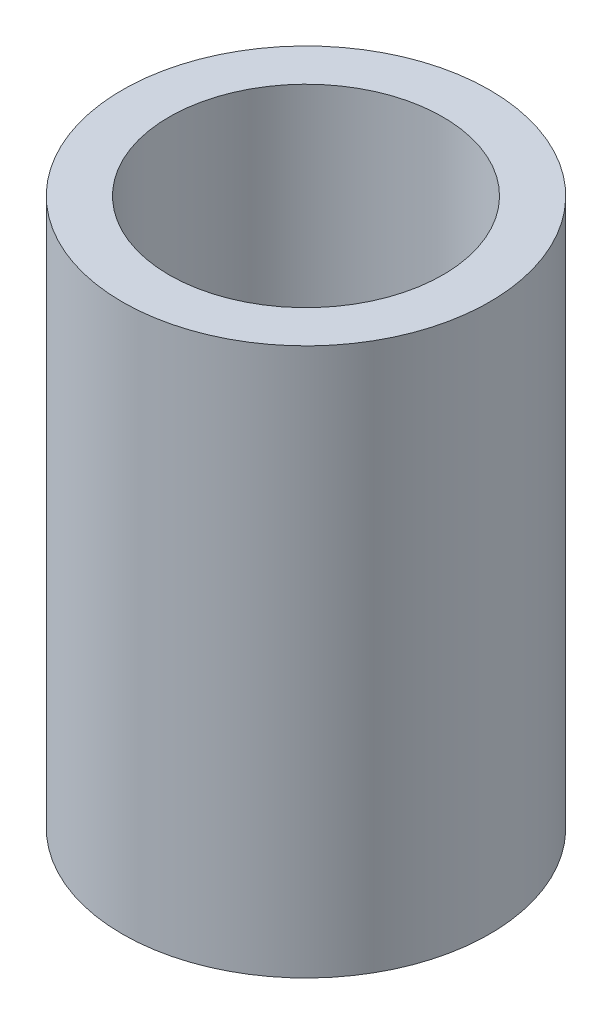
SolidWorks part; units mm, degrees
ref_plane "Front Plane" through (0, 0, 0) normal (0, 0, 1) x (1, 0, 0)
ref_plane "Top Plane" through (0, 0, 0) normal (0, 1, 0) x (1, 0, 0)
ref_plane "Right Plane" through (0, 0, 0) normal (1, 0, 0) x (0, 0, -1)
sketch "Sketch1" plane through (0, 0, 0) normal (0, 0, 1) x (1, 0, 0)
  line L0 (0, 0) -> (0, -62.5229) construction
  line L1 (-38.1, 0) -> (-51.1302, 0)
  line L2 (-38.1, 0) -> (-38.1, -152.4)
  line L3 (-38.1, -152.4) -> (-51.1302, -152.4)
  line L4 (-51.1302, 0) -> (-51.1302, -152.4)
  dimension "D1" = 38.1
  dimension "D2" = 51.1302
  dimension "D3" = 152.4
revolve "Revolve1" add sketch "Sketch1" angle 360 about L0
